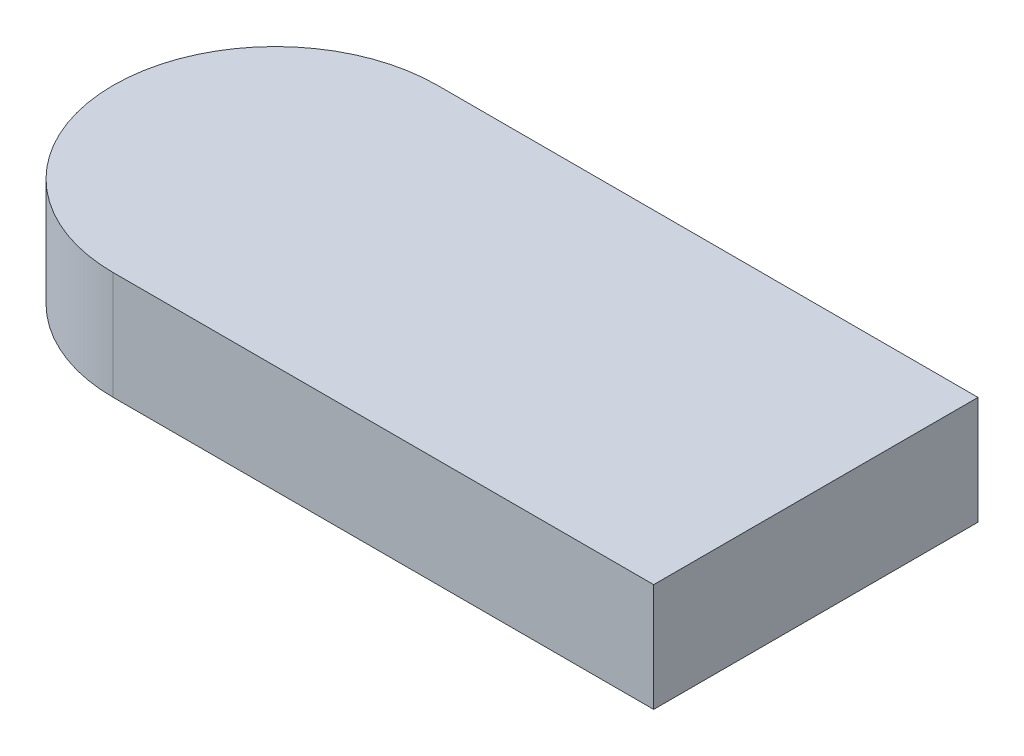
SolidWorks part; units mm, degrees
ref_plane "Front Plane" through (0, 0, 0) normal (0, 0, 1) x (1, 0, 0)
ref_plane "Top Plane" through (0, 0, 0) normal (0, 1, 0) x (1, 0, 0)
ref_plane "Right Plane" through (0, 0, 0) normal (1, 0, 0) x (0, 0, -1)
sketch "Sketch1" plane through (0, 0, 0) normal (0, 1, 0) x (1, 0, 0)
  line L1 (-75, 45) -> (75, 45)
  line L3 (-75, -45) -> (75, -45)
  line L4 (75, 45) -> (75, -45)
  line L5 (-75, 45) -> (75, -45) construction
  line L6 (-75, -45) -> (75, 45) construction
  arc A0 (-75, 45) -> (-75, -45) centre (-75, 0) ccw
  point P0 (0, 0)
  dimension "D1" = 90
  dimension "D2" = 150
extrude "Boss-Extrude1" add sketch "Sketch1" along normal mid plane 30 contours L3 L4 L1 A0
